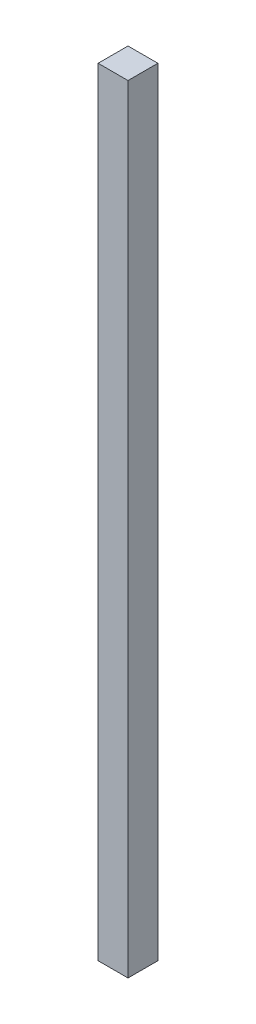
SolidWorks part; units mm, degrees
ref_plane "Front Plane" through (0, 0, 0) normal (0, 0, 1) x (1, 0, 0)
ref_plane "Top Plane" through (0, 0, 0) normal (0, 1, 0) x (1, 0, 0)
ref_plane "Right Plane" through (0, 0, 0) normal (1, 0, 0) x (0, 0, -1)
sketch "Sketch1" plane through (0, 0, 0) normal (0, 1, 0) x (1, 0, 0)
  line L1 (0, 0) -> (25.4, 0)
  line L2 (0, 0) -> (0, 25.4)
  line L3 (0, 25.4) -> (25.4, 25.4)
  line L4 (25.4, 0) -> (25.4, 25.4)
  dimension "D1" = 25.4
  dimension "D2" = 25.4
extrude "Boss-Extrude1" add sketch "Sketch1" along normal blind 660.4
